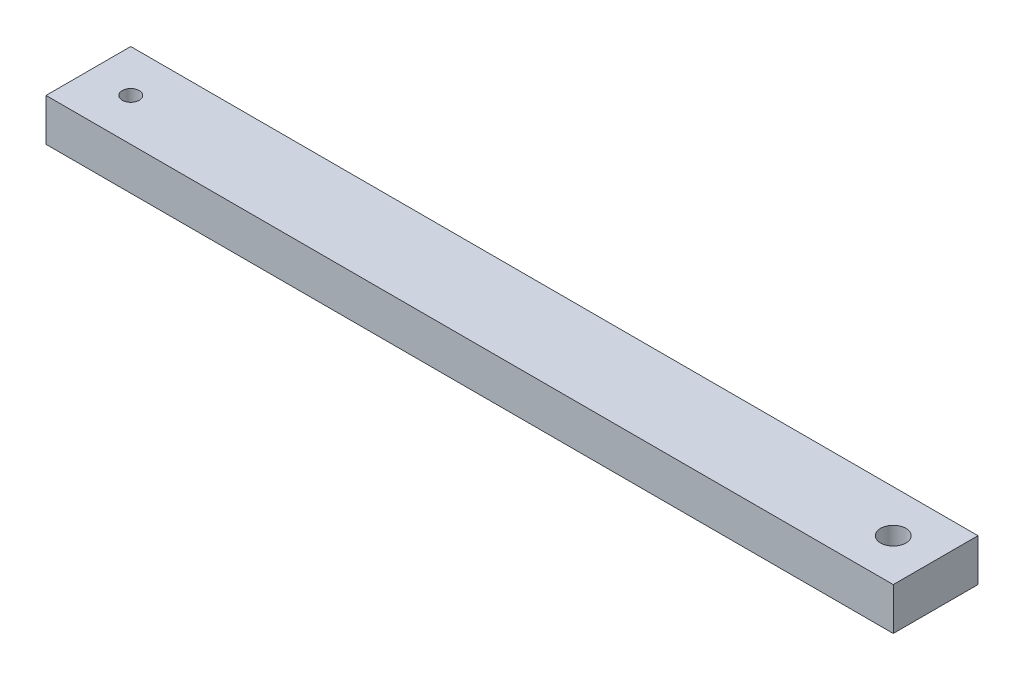
SolidWorks part; units mm, degrees
ref_plane "Alzado" through (0, 0, 0) normal (0, 0, 1) x (1, 0, 0)
ref_plane "Planta" through (0, 0, 0) normal (0, 1, 0) x (1, 0, 0)
ref_plane "Vista lateral" through (0, 0, 0) normal (1, 0, 0) x (0, 0, -1)
sketch "Croquis1" plane through (0, 0, 0) normal (0, 0, 1) x (1, 0, 0)
  line L1 (0, 5) -> (100, 5)
  line L2 (0, 5) -> (0, 0)
  line L3 (0, 0) -> (100, 0)
  line L4 (100, 5) -> (100, 0)
  dimension "D1" = 5
  dimension "D2" = 100
extrude "Saliente-Extruir1" add sketch "Croquis1" along normal blind 10
sketch "Croquis2" plane through (0, 5, 0) normal (0, 1, 0) x (1, 0, 0)
  line L0 (0, -5) -> (100, -5) construction
  line L1 (0, -10) -> (0, 0) construction
  line L2 (100, -10) -> (100, 0) construction
  circle A0 centre (5, -5) radius 1
  circle A1 centre (95, -5) radius 1.5
  dimension "D1" = 2
  dimension "D4" = 3
  dimension "D2" = 5
  dimension "D3" = 5
extrude "Cortar-Extruir1" cut sketch "Croquis2" against normal blind 10
